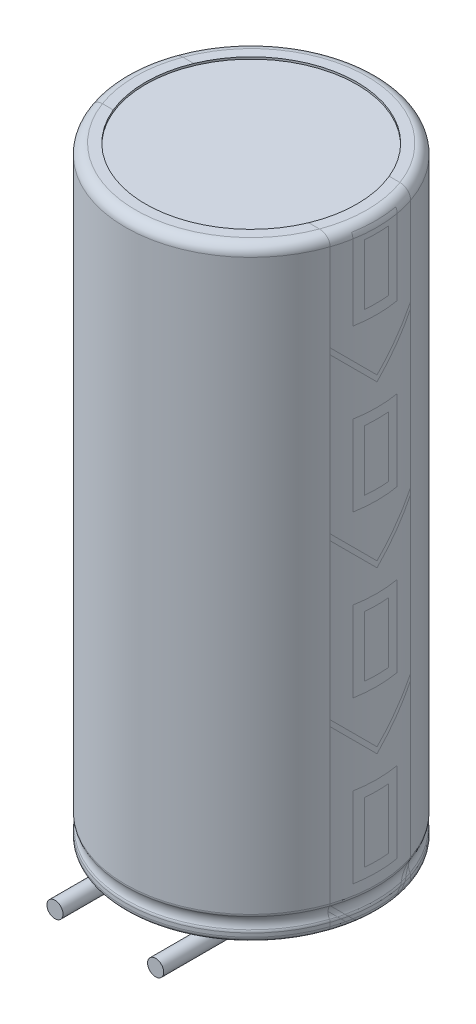
SolidWorks part; units mm, degrees
ref_plane "Front Plane" through (0, 0, 0) normal (0, 0, 1) x (1, 0, 0)
ref_plane "Top Plane" through (0, 0, 0) normal (0, 1, 0) x (1, 0, 0)
ref_plane "Right Plane" through (0, 0, 0) normal (1, 0, 0) x (0, 0, -1)
sketch "Sketch1" plane through (0, 0, 0) normal (0, 0, 1) x (1, 0, 0)
  line L0 (0, 0) -> (0, 58.059) construction
  line L1 (0, 29.9) -> (5.25, 29.9)
  line L2 (5.25, 29.9) -> (5.25, 30)
  line L3 (5.25, 30) -> (5.75, 30)
  line L4 (6.25, 29.5) -> (6.25, 1.2317)
  line L5 (0, 0) -> (6, 0)
  line L6 (6.25, 0.25) -> (6.25, 0.4317)
  line L7 (0, 0) -> (0, 29.9)
  arc A0 (6.2206, 0.5493) -> (6.2206, 1.114) centre (6.75, 0.8317) cw
  arc A1 (6.25, 1.2317) -> (6.2206, 1.114) centre (6, 1.2317) cw
  arc A2 (6.2206, 0.5493) -> (6.25, 0.4317) centre (6, 0.4317) cw
  arc A3 (6, 0) -> (6.25, 0.25) centre (6, 0.25) ccw
  arc A4 (6.25, 29.5) -> (5.75, 30) centre (5.75, 29.5) ccw
  point P15 (6.25, 0.5)
  point P18 (6.25, 0)
  dimension "D5" = 0.6
  dimension "D8" = 0.5
  dimension "D9" = 0.25
  dimension "D1" = 30
  dimension "D2" = 0.1
  dimension "D3" = 1
  dimension "D4" = 6.25
  dimension "D6" = 0.5
  dimension "D7" = 0.5
revolve "Revolve1" add sketch "Sketch1" angle 360 about L0
sketch "Sketch2" plane through (0, 0, 0) normal (1, 0, 0) x (0, 0, -1)
  line L0 (-6, 0) -> (6, 0) construction
  line L1 (-2, 30) -> (2, 30)
  line L2 (-2, 30) -> (-2, 0)
  line L3 (-2, 0) -> (2, 0)
  line L4 (2, 30) -> (2, 0)
  line L5 (5.25, 30) -> (-5.25, 30) construction
  dimension "D1" = 4
split line "Split Line1"
sketch "Sketch3" plane through (0, 0, 0) normal (1, 0, 0) x (0, 0, -1)
  line L0 (-1.1, 21.75) -> (1.1, 21.75)
  line L1 (-1.1, 29.75) -> (1.1, 29.75)
  line L2 (-1.1, 29.75) -> (-1.1, 25.75)
  line L3 (-1.1, 25.75) -> (1.1, 25.75)
  line L4 (1.1, 29.75) -> (1.1, 25.75)
  line L5 (-0.6, 29.25) -> (0.6, 29.25)
  line L6 (-0.6, 29.25) -> (-0.6, 26.25)
  line L7 (-0.6, 26.25) -> (0.6, 26.25)
  line L8 (0.6, 29.25) -> (0.6, 26.25)
  line L9 (-1.1, 21.75) -> (-1.1, 17.75)
  line L10 (-1.1, 17.75) -> (1.1, 17.75)
  line L11 (1.1, 21.75) -> (1.1, 17.75)
  line L12 (-0.6, 21.25) -> (0.6, 21.25)
  line L13 (-0.6, 21.25) -> (-0.6, 18.25)
  line L14 (-0.6, 18.25) -> (0.6, 18.25)
  line L15 (0.6, 21.25) -> (0.6, 18.25)
  line L16 (-1.1, 13.75) -> (1.1, 13.75)
  line L17 (-1.1, 13.75) -> (-1.1, 9.75)
  line L18 (-1.1, 9.75) -> (1.1, 9.75)
  line L19 (1.1, 13.75) -> (1.1, 9.75)
  line L20 (-0.6, 13.25) -> (0.6, 13.25)
  line L21 (-0.6, 13.25) -> (-0.6, 10.25)
  line L22 (-0.6, 10.25) -> (0.6, 10.25)
  line L23 (0.6, 13.25) -> (0.6, 10.25)
  line L24 (-1.1, 5.75) -> (1.1, 5.75)
  line L25 (-1.1, 5.75) -> (-1.1, 1.75)
  line L26 (-1.1, 1.75) -> (1.1, 1.75)
  line L27 (1.1, 5.75) -> (1.1, 1.75)
  line L28 (-0.6, 5.25) -> (0.6, 5.25)
  line L29 (-0.6, 5.25) -> (-0.6, 2.25)
  line L30 (-0.6, 2.25) -> (0.6, 2.25)
  line L31 (0.6, 5.25) -> (0.6, 2.25)
  line L32 (0, 0) -> (0, 1.75) construction
  line L33 (0, 1.75) -> (0, 2.25) construction
  line L34 (5.25, 30) -> (2, 30) construction
  line L35 (-2, 25.15) -> (-2, 24.85)
  line L36 (-2, 1.2317) -> (-2, 29.5) construction
  line L37 (-2, 24.85) -> (0, 22.85)
  line L38 (0, 22.85) -> (2, 24.85)
  line L39 (2, 29.5) -> (2, 1.2317) construction
  line L40 (2, 24.85) -> (2, 25.15)
  line L41 (2, 25.15) -> (0, 23.15)
  line L42 (0, 23.15) -> (-2, 25.15)
  line L43 (2, 25.15) -> (-2, 25.15) construction
  line L44 (0, 23.15) -> (0, 22.85) construction
  line L45 (0, 21.75) -> (0, 22.85) construction
  line L46 (2, 16.85) -> (2, 17.15)
  line L47 (2, 17.15) -> (0, 15.15)
  line L48 (0, 14.85) -> (2, 16.85)
  line L49 (-2, 16.85) -> (0, 14.85)
  line L50 (0, 15.15) -> (-2, 17.15)
  line L51 (-2, 17.15) -> (-2, 16.85)
  line L52 (2, 8.85) -> (2, 9.15)
  line L53 (2, 9.15) -> (0, 7.15)
  line L54 (0, 6.85) -> (2, 8.85)
  line L55 (-2, 8.85) -> (0, 6.85)
  line L56 (0, 7.15) -> (-2, 9.15)
  line L57 (-2, 9.15) -> (-2, 8.85)
  line L58 (2, 0.85) -> (2, 1.15)
  line L59 (2, 1.15) -> (0, -0.85)
  line L60 (0, -1.15) -> (2, 0.85)
  line L61 (-2, 0.85) -> (0, -1.15)
  line L62 (0, -0.85) -> (-2, 1.15)
  line L63 (-2, 1.15) -> (-2, 0.85)
  dimension "D1" = 4
  dimension "D2" = 3
  dimension "D3" = 2.2
  dimension "D4" = 1.2
  dimension "D5" = 0.5
  dimension "D6" = 0.5
  dimension "D7" = 0.5
  dimension "D8" = 0.5
  dimension "D9" = 0.25
  dimension "D10" = 4
  dimension "D11" = 4
  dimension "D12" = 4
  dimension "D13" = 0.3
  dimension "D14" = 0.3
  dimension "D15" = 90
  dimension "D16" = 2.6
  dimension "D17" = 4
  dimension "D18" = 1.1
split line "Split Line2"
sketch "Sketch4" plane through (0, 0, 0) normal (0, -1, 0) x (1, 0, 0)
  line L1 (0, 0) -> (-2.5, 0) construction
  circle A1 centre (-2.5, 0) radius 0.4
  dimension "D1" = 2.5
  dimension "D2" = 0.8
ref_plane "Plane1" through (-2.5, 0, 0) normal (1, 0, 0) x (0, 0, -1)
sketch "Sketch5" plane through (-2.5, 0, 0) normal (1, 0, 0) x (0, 0, -1)
  line L0 (0, 0) -> (0, -0.1)
  line L1 (0.5, -0.6) -> (7.25, -0.6) construction
  line L2 (6.25, 1.2317) -> (6.25, 29.5) construction
  line L3 (2, 0) -> (6, 0) construction
  line L4 (-0.5, -0.6) -> (-7.25, -0.6)
  arc A0 (0, -0.1) -> (0.5, -0.6) centre (0.5, -0.1) ccw construction
  arc A1 (-0.5, -0.6) -> (0, -0.1) centre (-0.5, -0.1) ccw
  dimension "D1" = 0.5
  dimension "D2" = 1
  dimension "D3" = 0.6
sweep "Sweep1" add profiles "Sketch5" path "Sketch4"
mirror "Mirror1" about plane through (0, 0, 0) normal (1, 0, 0) of "Sweep1"
